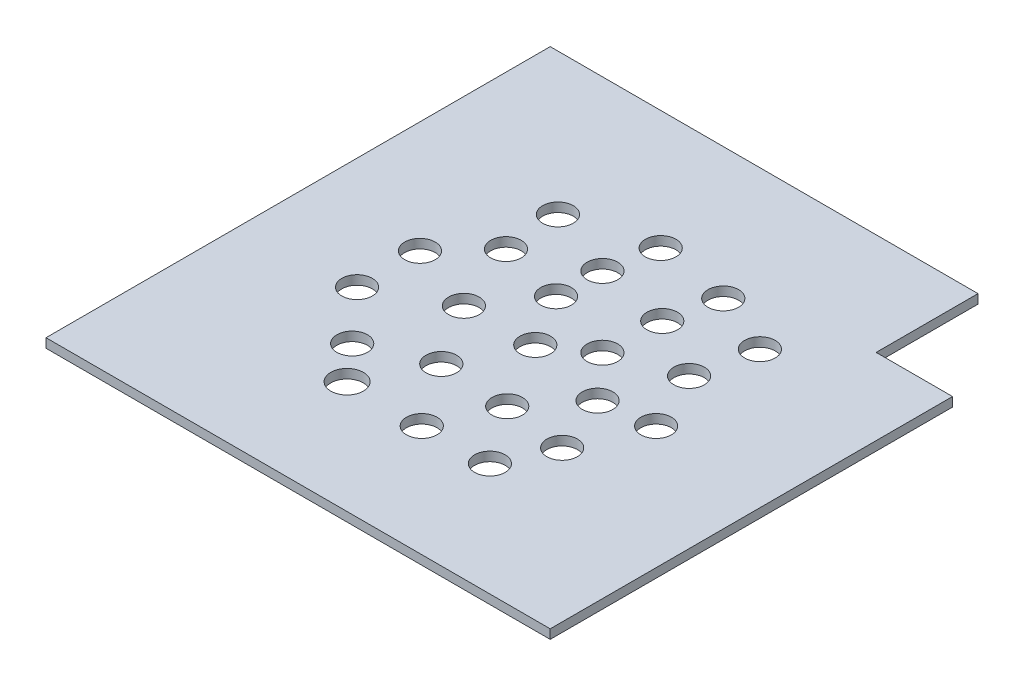
SolidWorks part; units mm, degrees
ref_plane "前视基准面" through (0, 0, 0) normal (0, 0, 1) x (1, 0, 0)
ref_plane "上视基准面" through (0, 0, 0) normal (0, 1, 0) x (1, 0, 0)
ref_plane "右视基准面" through (0, 0, 0) normal (1, 0, 0) x (0, 0, -1)
sketch "草图1" plane through (0, 0, 0) normal (0, 1, 0) x (1, 0, 0)
  line L1 (0, 0) -> (99, 0)
  line L2 (0, 0) -> (0, 99)
  line L3 (0, 99) -> (99, 99)
  line L4 (99, 0) -> (99, 99)
  dimension "D1" = 99
  dimension "D2" = 99
extrude "凸台-拉伸1" add sketch "草图1" along normal blind 1.8
sketch "草图2" plane through (0, 1.8, 0) normal (0, 1, 0) x (1, 0, 0)
  circle A0 centre (29.2982, 71.2241) radius 3
  circle A1 centre (45.102, 75.5953) radius 3
  circle A2 centre (30.0922, 60.2288) radius 3
  circle A3 centre (35.6051, 46.4504) radius 3
  circle A4 centre (43.2752, 34.3422) radius 3
  circle A5 centre (56.9376, 33.6231) radius 3
  circle A6 centre (49.2675, 46.8061) radius 3
  circle A7 centre (64.8474, 43.4504) radius 3
  circle A8 centre (69.6412, 56.6334) radius 3
  circle A9 centre (57.6567, 63.3448) radius 3
  circle A10 centre (43.0355, 57.1128) radius 3
  circle A11 centre (43.2752, 65.9814) radius 3
  circle A12 centre (59.8139, 73.1721) radius 3
  circle A13 centre (69.4015, 31.9453) radius 3
  circle A14 centre (31.051, 29.069) radius 3
  circle A15 centre (51.9041, 21.8783) radius 3
  circle A16 centre (21.9427, 39.136) radius 3
  circle A17 centre (21.9427, 51.4839) radius 3
  circle A18 centre (74.9144, 44.8886) radius 3
  circle A19 centre (64.9866, 22.1759) radius 3
  circle A20 centre (37.0433, 22.0761) radius 3.1979
  circle A21 centre (72.0381, 68.1386) radius 3
  circle A22 centre (57.1773, 52.0793) radius 3
  dimension "D1" = 6
  dimension "D2" = 6
extrude "切除-拉伸1" cut sketch "草图2" against normal through all
sketch "草图3" plane through (0, 1.8, 0) normal (0, 1, 0) x (1, 0, 0)
  line L1 (99, 99) -> (84, 99)
  line L2 (99, 99) -> (99, 79)
  line L3 (99, 79) -> (84, 79)
  line L4 (84, 99) -> (84, 79)
  dimension "D1" = 15
  dimension "D2" = 20
extrude "切除-拉伸2" cut sketch "草图3" against normal through all
